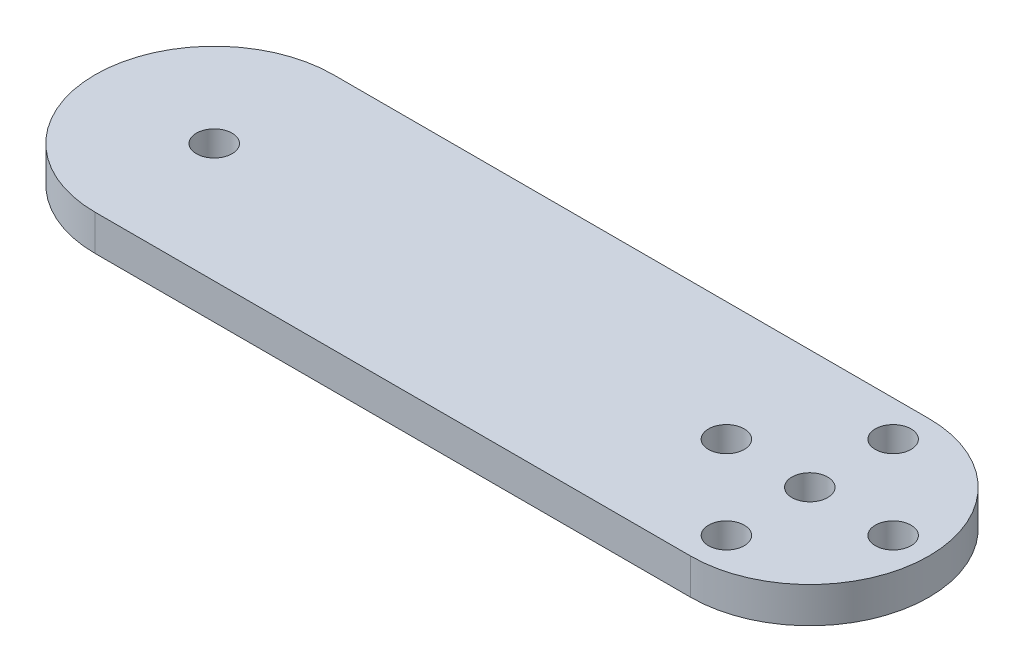
SolidWorks part; units mm, degrees
ref_plane "Front Plane" through (0, 0, 0) normal (0, 0, 1) x (1, 0, 0)
ref_plane "Top Plane" through (0, 0, 0) normal (0, 1, 0) x (1, 0, 0)
ref_plane "Right Plane" through (0, 0, 0) normal (1, 0, 0) x (0, 0, -1)
sketch "Sketch1" plane through (0, 0, 0) normal (0, 1, 0) x (1, 0, 0)
  line L0 (-25, 20) -> (-25, 0) construction
  line L1 (0, 0) -> (-50, 0)
  line L3 (0, 20) -> (-50, 20)
  line L5 (-10, 10) -> (10, 10) construction
  line L6 (0, 20) -> (0, 0) construction
  arc A0 (0, 0) -> (0, 20) centre (0, 10) ccw
  arc A1 (-50, 0) -> (-50, 20) centre (-50, 10) cw
  circle A2 centre (0, 10) radius 1.5
  circle A3 centre (0, 17) radius 1.5
  circle A4 centre (0, 3) radius 1.5
  circle A5 centre (7, 10) radius 1.5
  circle A6 centre (-7, 10) radius 1.5
  circle A7 centre (-50, 10) radius 1.5
  dimension "D3" = 20
  dimension "D4" = 3
  dimension "D6" = 3
  dimension "D7" = 3
  dimension "D9" = 3
  dimension "D1" = 50
  dimension "D2" = 20
  dimension "D5" = 7
  dimension "D8" = 7
extrude "Boss-Extrude1" add sketch "Sketch1" along normal blind 3 contours L3 A1 L1 A0 | A7 | A4 | A2 | A5 | A3 | A6
